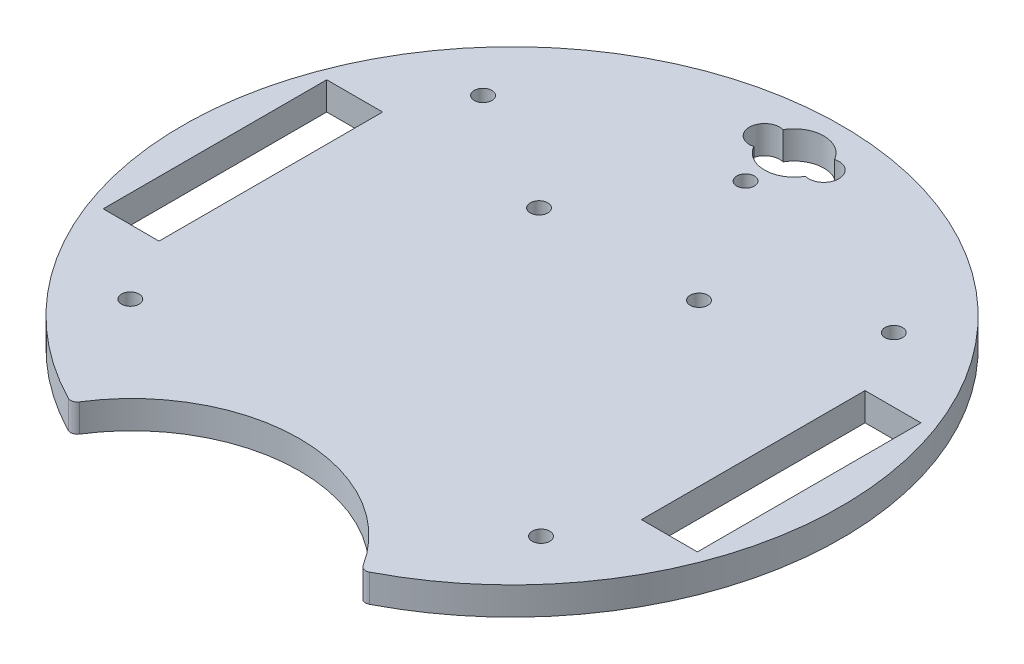
SolidWorks part; units mm, degrees
ref_plane "Front Plane" through (0, 0, 0) normal (0, 0, 1) x (1, 0, 0)
ref_plane "Top Plane" through (0, 0, 0) normal (0, 1, 0) x (1, 0, 0)
ref_plane "Right Plane" through (0, 0, 0) normal (1, 0, 0) x (0, 0, -1)
sketch "Sketch1" plane through (0, 0, 0) normal (0, 1, 0) x (1, 0, 0)
  line L1 (0, 86.2583) -> (0, -96.8543) construction
  line L3 (-32.9956, -67.352) -> (0, -86.402) construction
  line L4 (32.9956, -67.352) -> (0, -86.402) construction
  line L9 (54.8141, -25.4) -> (54.8141, 25.4)
  line L10 (-67.5141, -25.4) -> (-54.8141, -25.4)
  line L11 (-67.5141, -25.4) -> (-67.5141, 25.4)
  line L12 (-67.5141, 25.4) -> (-54.8141, 25.4)
  line L13 (-54.8141, 25.4) -> (-54.8141, -25.4)
  line L14 (67.5141, 25.4) -> (54.8141, 25.4)
  line L15 (67.5141, -25.4) -> (67.5141, 25.4)
  line L16 (67.5141, -25.4) -> (54.8141, -25.4)
  arc A1 (32.2407, -66.1006) -> (-32.2407, -66.1006) centre (0, -86.402) ccw
  arc A2 (34.1948, -66.6358) -> (-34.1948, -66.6358) centre (0, 0) ccw
  arc A3 (5.8576, 67.4236) -> (-5.8539, 67.4301) centre (0, 64.1077) ccw
  arc A4 (-5.8539, 67.4301) -> (-5.8539, 60.7853) centre (-6.731, 64.1077) ccw
  arc A5 (5.8576, 60.7918) -> (5.8576, 67.4236) centre (6.731, 64.1077) ccw
  arc A6 (-5.8539, 60.7853) -> (5.8576, 60.7918) centre (0, 64.1077) ccw
  circle A25 centre (-18.179, 24.3106) radius 2
  circle A38 centre (-46.6637, -40.0812) radius 2
  circle A39 centre (46.6637, -40.0812) radius 2
  circle A40 centre (46.6637, 40.0812) radius 2
  circle A41 centre (-46.6637, 40.0812) radius 2
  arc A42 (-34.1948, -66.6358) -> (-32.2407, -66.1006) centre (-33.51, -65.3013) ccw
  arc A43 (34.1948, -66.6358) -> (32.2407, -66.1006) centre (33.51, -65.3013) cw
  circle A44 centre (-6.731, 64.1077) radius 1.143
  circle A45 centre (6.731, 64.1077) radius 1.143
  circle A47 centre (18.179, 24.3106) radius 2
  circle A48 centre (0, 53.0612) radius 2
  dimension "D3" = 120
  dimension "D15" = 13.462
  dimension "D18" = 2.286
  dimension "D12" = 4
  dimension "D4" = 50.8
  dimension "D5" = 12.7
extrude "Boss-Extrude3" add sketch "Sketch1" along normal blind 6.35 contours A43 A2 A42 A1 A48 A47 A40 A39 A38 L15 L16 L9 L14 L12 L13 L10 L11 A6 A4 A3 A5 A25 A41
